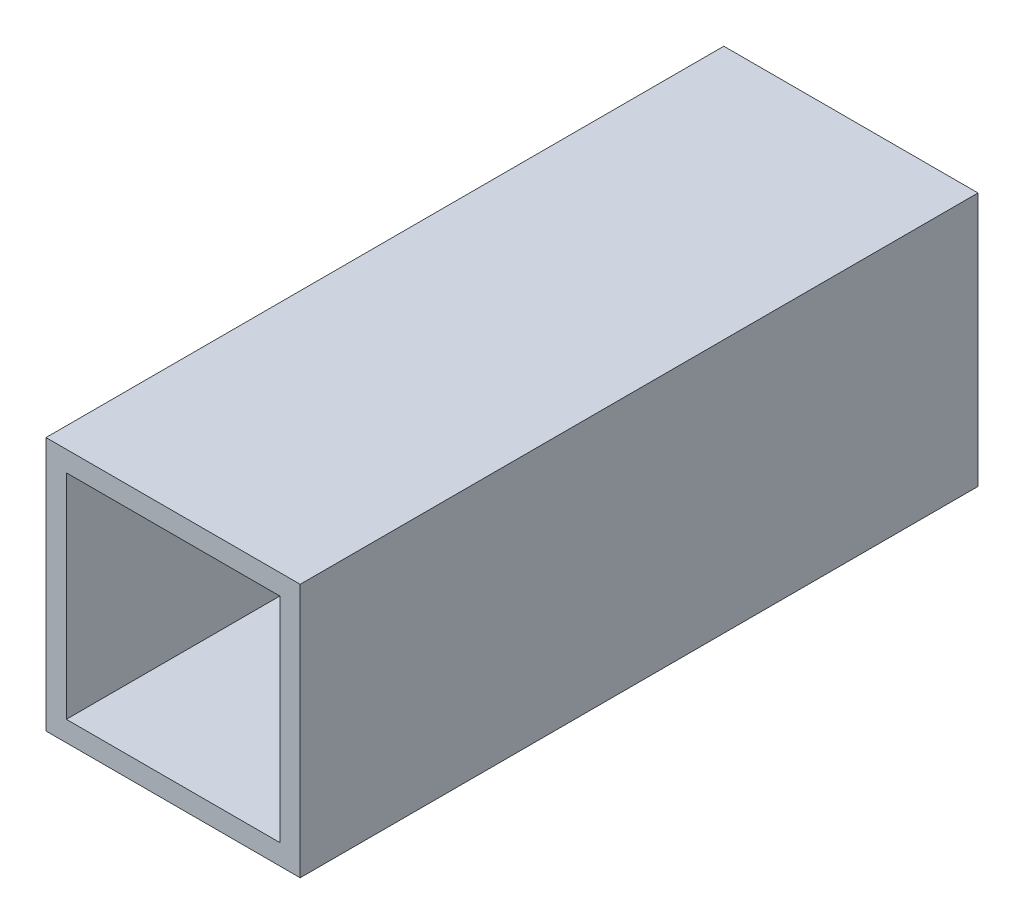
SolidWorks part; units mm, degrees
ref_plane "Front Plane" through (0, 0, 0) normal (0, 0, 1) x (1, 0, 0)
ref_plane "Top Plane" through (0, 0, 0) normal (0, 1, 0) x (1, 0, 0)
ref_plane "Right Plane" through (0, 0, 0) normal (1, 0, 0) x (0, 0, -1)
sketch "Sketch1" plane through (0, 0, 0) normal (0, 0, 1) x (1, 0, 0)
  line L5 (-16.002, 16.002) -> (16.002, 16.002)
  line L6 (-16.002, 16.002) -> (-16.002, -16.002)
  line L11 (-16.002, -16.002) -> (16.002, -16.002)
  line L12 (16.002, 16.002) -> (16.002, -16.002)
  line L13 (-16.002, 16.002) -> (16.002, -16.002) construction
  line L14 (-16.002, -16.002) -> (16.002, 16.002) construction
  line L15 (19.05, -19.05) -> (-19.05, -19.05)
  line L16 (19.05, -19.05) -> (19.05, 19.05)
  line L17 (19.05, 19.05) -> (-19.05, 19.05)
  line L18 (-19.05, -19.05) -> (-19.05, 19.05)
  line L19 (19.05, -19.05) -> (-19.05, 19.05) construction
  line L20 (19.05, 19.05) -> (-19.05, -19.05) construction
  point P0 (0, 0)
  point P6 (0, 0)
  dimension "D1" = 3.048
  dimension "D2" = 38.1
extrude "Boss-Extrude1" add sketch "Sketch1" along normal mid plane 101.6
